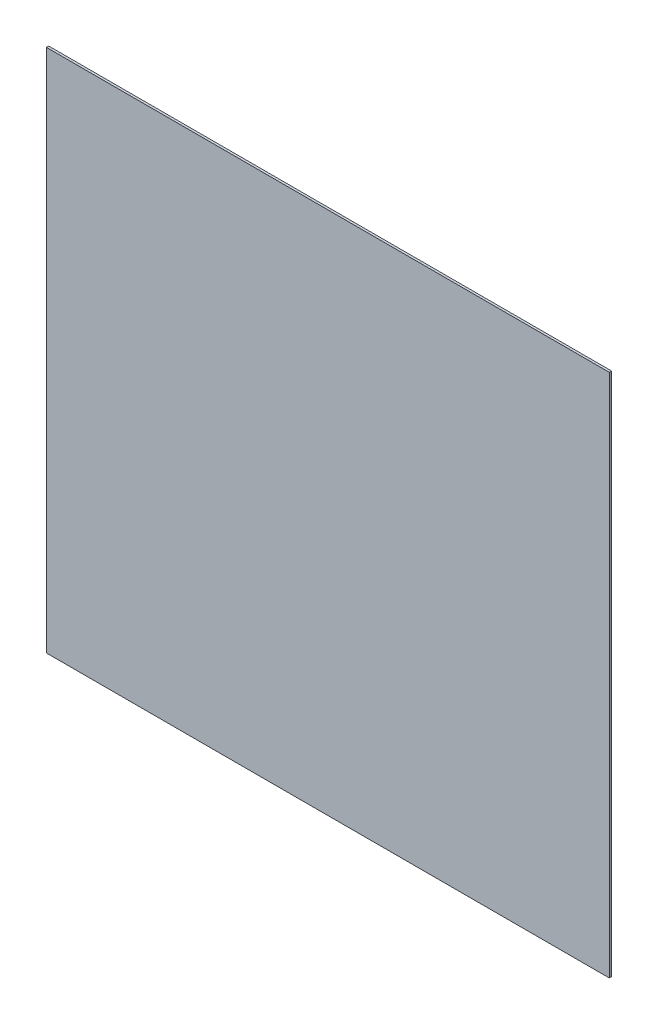
SolidWorks part; units mm, degrees
material "Mahogany"
ref_plane "Front Plane" through (0, 0, 0) normal (0, 0, 1) x (1, 0, 0)
ref_plane "Top Plane" through (0, 0, 0) normal (0, 1, 0) x (1, 0, 0)
ref_plane "Right Plane" through (0, 0, 0) normal (1, 0, 0) x (0, 0, -1)
sketch "Sketch1" plane through (0, 0, 0) normal (0, 0, 1) x (1, 0, 0)
  line L1 (-389, -362.5) -> (389, -362.5)
  line L2 (-389, -362.5) -> (-389, 362.5)
  line L3 (-389, 362.5) -> (389, 362.5)
  line L4 (389, -362.5) -> (389, 362.5)
  line L5 (-389, -362.5) -> (389, 362.5) construction
  line L6 (-389, 362.5) -> (389, -362.5) construction
  point P0 (0, 0)
  dimension "D1" = 778
  dimension "D2" = 725
extrude "Boss-Extrude1" add sketch "Sketch1" along normal blind 3.175
equation "\"W\"= 1700"
equation "\"L\"= 760"
equation "\"H\"= 810"
equation "\"ARM_BOLT_SPACING\"= 166"
equation "\"ARM_TO_WALL\"= 300"
equation "\"D1@Sketch1\"=(\"W\"/2)-72"
equation "\"D2@Sketch1\"=\"H\"-85"
